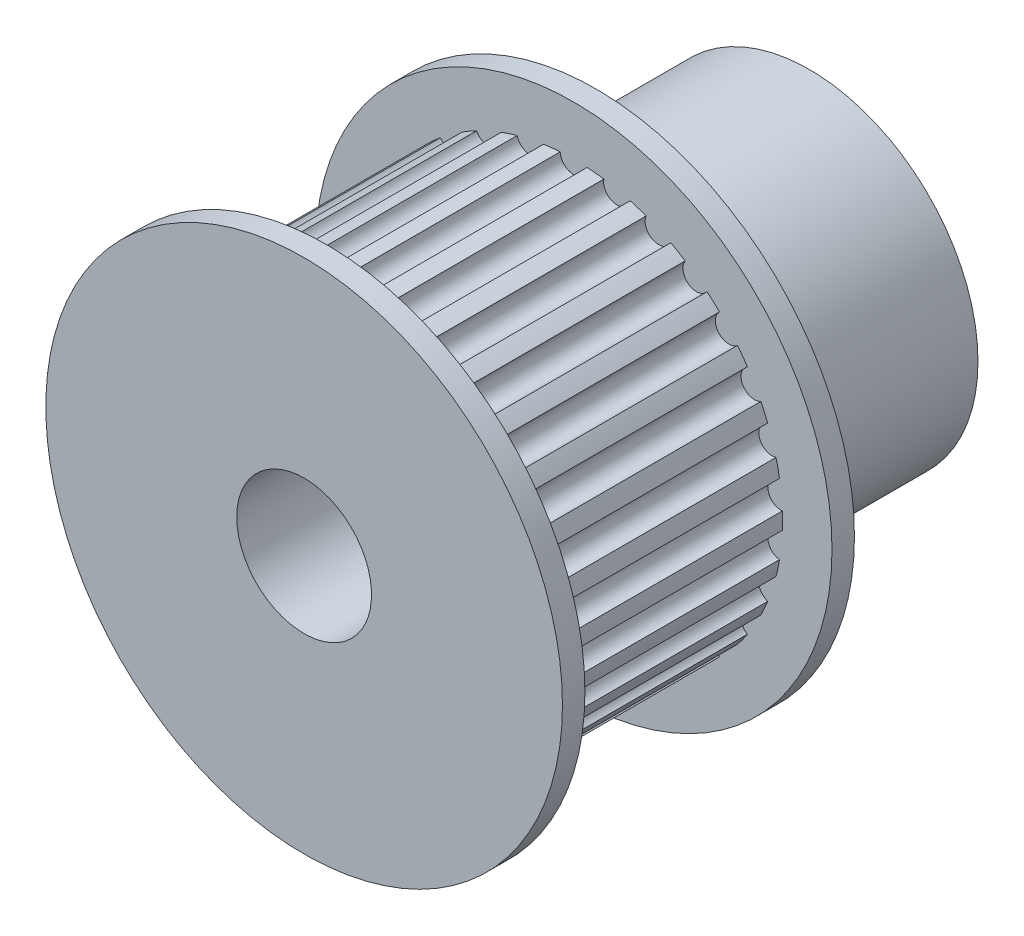
SolidWorks part; units mm, degrees
material "6061 合金"
ref_plane "前基準面" through (0, 0, 0) normal (0, 0, 1) x (1, 0, 0)
ref_plane "上基準面" through (0, 0, 0) normal (0, 1, 0) x (1, 0, 0)
ref_plane "右基準面" through (0, 0, 0) normal (1, 0, 0) x (0, 0, -1)
sketch "草圖1" plane through (0, 0, 0) normal (0, 0, 1) x (1, 0, 0)
  circle A0 centre (0, 0) radius 11.5
  dimension "D1" = 23
extrude "填料-伸長1" add sketch "草圖1" along normal mid plane 1
sketch "草圖2" plane through (0, 0, 0.5) normal (0, 0, 1) x (1, 0, 0)
  circle A0 centre (0, 0) radius 9.295
  dimension "D1" = 18.59
extrude "填料-伸長2" add sketch "草圖2" along normal blind 11
sketch "草圖8" plane through (0, 0, 0) normal (0, 0, -1) x (-1, 0, 0)
  circle A0 centre (0, 0) radius 7.5
  dimension "D1" = 15
extrude "填料-伸長4" add sketch "草圖8" along normal blind 10
sketch "草圖7" plane through (0, 0, 11.5) normal (0, 0, 1) x (1, 0, 0)
  line L0 (0, 0) -> (0, 9.295) construction
  arc A0 (-0.5997, 9.2756) -> (0.5997, 9.2756) centre (0, 9.295) ccw
  circle A1 centre (0, 0) radius 9.295 construction
  circle A2 centre (0, 0) radius 9.295 construction
  arc A3 (-0.5997, 9.2756) -> (0.5997, 9.2756) centre (0, 0) cw
  point P10 (0, 8.695)
  dimension "D1" = 0.6
extrude "除料-伸長3" cut sketch "草圖7" against normal up to surface (11 mm away) up to face at (9.295, 0, 0.5)
sketch "草圖3" plane through (0, 0, 11.5) normal (0, 0, 1) x (1, 0, 0)
  circle A0 centre (0, 0) radius 11.5
  circle A1 centre (0, 0) radius 11.5 construction
extrude "填料-伸長3" add sketch "草圖3" along normal blind 1
sketch "草圖6" plane through (0, 0, -0.5) normal (0, 0, -1) x (-1, 0, 0)
  circle A0 centre (0, 0) radius 3
  dimension "D1" = 6
extrude "除料-伸長2" cut sketch "草圖6" against normal through all both and the other way through all
pattern_circular "環狀複製排列2" count 30 over 360 about axis through (0, 0, 0) along (0, 0, 1) of "除料-伸長3"
